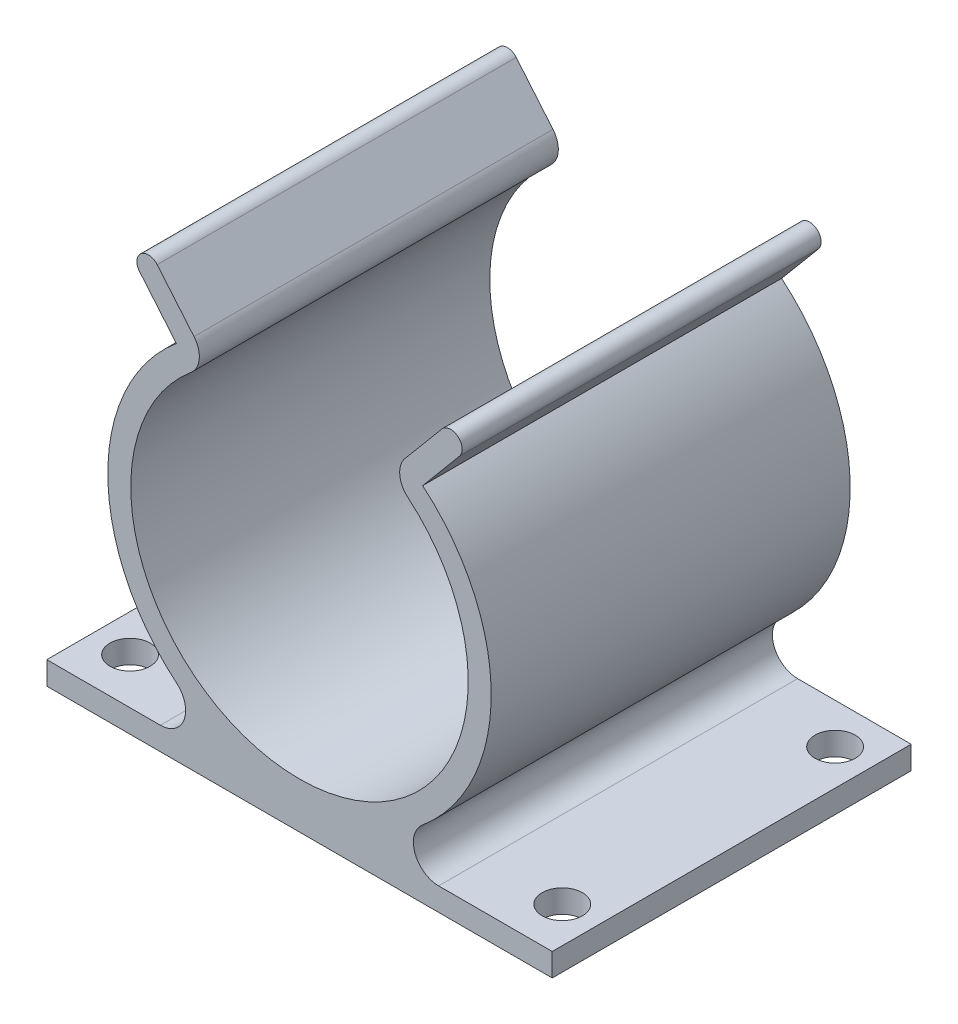
SolidWorks part; units mm, degrees
ref_plane "Front" through (0, 0, 0) normal (0, 0, 1) x (1, 0, 0)
ref_plane "Top" through (0, 0, 0) normal (0, 1, 0) x (1, 0, 0)
ref_plane "Right" through (0, 0, 0) normal (1, 0, 0) x (0, 0, -1)
sketch "Sketch1" plane through (0, 0, 0) normal (0, 0, 1) x (1, 0, 0)
  line L0 (0, 0) -> (0, 25.1763) construction
  line L1 (-17.6, 0.8) -> (-9.6888, 0.8)
  line L2 (-17.6, 0.8) -> (-17.6, -0.8)
  line L3 (-17.6, -0.8) -> (17.6, -0.8)
  line L4 (17.6, 0.8) -> (17.6, -0.8)
  line L5 (-17.6, 0.8) -> (17.6, -0.8) construction
  line L6 (-17.6, -0.8) -> (17.6, 0.8) construction
  line L7 (9.6888, 0.8) -> (17.6, 0.8)
  line L8 (0, 14.15) -> (7.5476, 23.1553) construction
  line L10 (8.5754, 24.3816) -> (11.1376, 27.4387)
  line L11 (-8.5754, 24.3816) -> (-11.1376, 27.4387) construction
  line L12 (-7.3491, 25.4094) -> (-9.9113, 28.4665)
  line L13 (7.3491, 25.4094) -> (9.9113, 28.4665)
  line L14 (8.5754, 24.3816) -> (11.1376, 27.4387) construction
  line L15 (-8.5754, 24.3816) -> (-11.1376, 27.4387)
  arc A0 (-7.5476, 23.1553) -> (7.5476, 23.1553) centre (0, 14.15) ccw
  arc A1 (8.5615, 3.9068) -> (8.5754, 24.3816) centre (0, 14.15) ccw
  arc A2 (-9.6888, 0.8) -> (-8.5615, 3.9068) centre (-9.6888, 2.5579) ccw
  arc A3 (8.5615, 3.9068) -> (9.6888, 0.8) centre (9.6888, 2.5579) ccw
  arc A4 (-8.5754, 24.3816) -> (-8.5615, 3.9068) centre (0, 14.15) ccw
  arc A5 (7.3491, 25.4094) -> (7.5476, 23.1553) centre (8.5754, 24.3816) ccw
  arc A6 (11.1376, 27.4387) -> (9.9113, 28.4665) centre (10.5245, 27.9526) ccw
  arc A7 (-11.1376, 27.4387) -> (-9.9113, 28.4665) centre (-10.5245, 27.9526) cw
  arc A8 (-7.3491, 25.4094) -> (-7.5476, 23.1553) centre (-8.5754, 24.3816) cw
  point P0 (0, 0)
  dimension "D3" = 23.5
  dimension "D4" = 1.6
  dimension "D1" = 1.6
  dimension "D2" = 35.2
extrude "Boss-Extrude1" add sketch "Sketch1" along normal blind 25
sketch "Sketch3" plane through (0, -0.8, 0) normal (0, -1, 0) x (1, 0, 0)
  line L0 (0.05, 23.0192) -> (0.05, 21.8) construction
  line L1 (-15, 21.8) -> (-15, 25) construction
  line L2 (-15, 21.8) -> (15.1, 21.8) construction
  line L4 (-17.6, 25) -> (-17.6, 0) construction
  line L5 (-17.6, 25) -> (17.6, 25) construction
  line L6 (-15, 21.8) -> (-15, 2.8) construction
  line L7 (-15, 2.8) -> (15.1, 2.8) construction
  line L8 (15.1, 21.8) -> (15.1, 2.8) construction
  line L9 (-15, 21.8) -> (-17.6, 21.8) construction
  circle A0 centre (-15, 21.8) radius 1.4
  circle A1 centre (15.1, 21.8) radius 1.4
  circle A2 centre (-15, 2.8) radius 1.4
  circle A3 centre (15.1, 2.8) radius 1.4
  dimension "D1" = 19
  dimension "D2" = 30.1
  dimension "D3" = 3.2
  dimension "D4" = 2.6
extrude "Cut-Extrude1" cut sketch "Sketch3" against normal up to next
